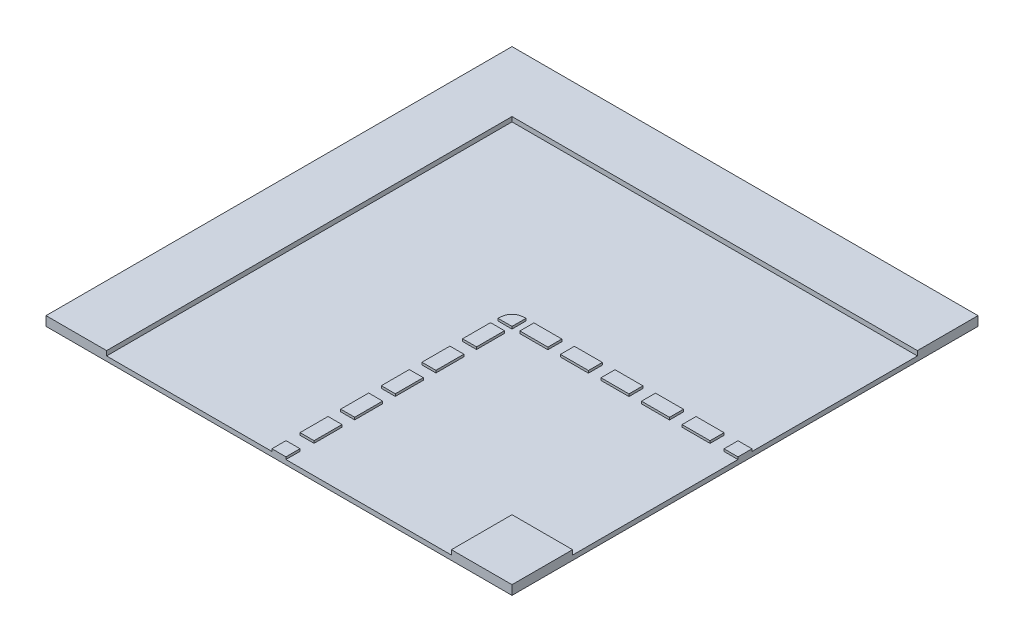
SolidWorks part; units mm, degrees
ref_plane "Plano frontal" through (0, 0, 0) normal (0, 0, 1) x (1, 0, 0)
ref_plane "Plano superior" through (0, 0, 0) normal (0, 1, 0) x (1, 0, 0)
ref_plane "Plano direito" through (0, 0, 0) normal (1, 0, 0) x (0, 0, -1)
sketch "Esboço1" plane through (0, 0, 0) normal (0, 1, 0) x (1, 0, 0)
  line L1 (-0.5, -0.5) -> (0.5, -0.5)
  line L2 (-0.5, -0.5) -> (-0.5, 0.5)
  line L3 (-0.5, 0.5) -> (0.5, 0.5)
  line L4 (0.5, -0.5) -> (0.5, 0.5)
  line L5 (-0.5, -0.5) -> (0.5, 0.5) construction
  line L6 (-0.5, 0.5) -> (0.5, -0.5) construction
  point P0 (0, 0)
  dimension "D1" = 1
  dimension "D2" = 1
sketch "Esboço2" plane through (0, 0, 0) normal (0, 1, 0) x (1, 0, 0)
  line L1 (0.5, 0.5) -> (-0.5, 0.5)
  line L2 (0.5, 0.5) -> (0.5, 0.37)
  line L3 (0.5, 0.37) -> (-0.37, 0.37)
  line L5 (-0.5, 0.5) -> (0.5, -0.5) construction
  line L6 (-0.5, -0.5) -> (-0.37, -0.5)
  line L7 (-0.5, -0.5) -> (-0.5, 0.5)
  line L8 (-0.5, 0.5) -> (-0.37, 0.5)
  line L9 (-0.37, -0.5) -> (-0.37, 0.37)
  line L10 (0.5, -0.5) -> (0.37, -0.5)
  line L11 (0.5, -0.5) -> (0.5, -0.37)
  line L12 (0.5, -0.37) -> (0.37, -0.37)
  line L13 (0.37, -0.5) -> (0.37, -0.37)
  dimension "D1" = 0.13
  dimension "D2" = 0.13
  dimension "D3" = 0.13
extrude "Ressalto-extrusão1" add sketch "Esboço1" along normal blind 0.01
extrude "Ressalto-extrusão2" add sketch "Esboço2" along normal blind 0.02 contours L7 L6 L9 L3 L2 L1 | L10 L13 L12 L11
sketch "Esboço3" plane through (0, 0.01, 0) normal (0, 1, 0) x (1, 0, 0)
  line L0 (0, 0) -> (0.4995, 0) construction
  line L1 (0, 0) -> (0, -0.5) construction
  line L2 (-0.37, -0.5) -> (0.37, -0.5) construction
  line L4 (-0.0152, -0.5) -> (-0.0152, -0.4698)
  line L5 (-0.0152, -0.4698) -> (0.0148, -0.4698)
  line L6 (0.0148, -0.5) -> (0.0148, -0.4698)
  line L7 (0, -0.5) -> (0.0148, -0.4698) construction
  line L8 (-0.0152, -0.4698) -> (0, -0.5) construction
  line L9 (-0.0152, -0.5) -> (0.0148, -0.5)
  line L10 (0, -0.53) -> (0, -0.6863) construction
  line L12 (-0.015, -0.3798) -> (0.015, -0.3798)
  line L13 (-0.015, -0.3798) -> (-0.015, -0.4398)
  line L14 (-0.015, -0.4398) -> (0.015, -0.4398)
  line L15 (0.015, -0.3798) -> (0.015, -0.4398)
  line L16 (-0.015, -0.3798) -> (0.015, -0.4398) construction
  line L17 (-0.015, -0.4398) -> (0.015, -0.3798) construction
  line L41 (-0.015, -0.015) -> (-0.015, 0.015) construction
  line L44 (-0.015, -0.015) -> (0.015, -0.015)
  line L45 (0.015, 0.015) -> (0.015, -0.015)
  line L46 (-0.015, 0.015) -> (0.015, 0.015) construction
  line L47 (0.47, 0.015) -> (0.5, 0.015)
  line L51 (0.47, -0.015) -> (0.47, 0.015)
  line L52 (0.4995, 0) -> (0.47, 0.015) construction
  line L53 (0.4995, 0) -> (0.47, -0.015) construction
  line L54 (0.5, -0.37) -> (0.5, 0.37) construction
  line L55 (0.47, -0.015) -> (0.5, -0.015)
  line L56 (0.5, -0.015) -> (0.5, 0.015)
  line L57 (0.293, -0.015) -> (0.293, 0.015)
  line L58 (0.38, -0.015) -> (0.44, -0.015)
  line L59 (0.38, -0.015) -> (0.38, 0.015)
  line L60 (0.38, 0.015) -> (0.44, 0.015)
  line L61 (0.44, -0.015) -> (0.44, 0.015)
  line L62 (0.38, -0.015) -> (0.44, 0.015) construction
  line L63 (0.38, 0.015) -> (0.44, -0.015) construction
  line L64 (0.293, -0.015) -> (0.353, -0.015)
  line L65 (0.353, -0.015) -> (0.353, 0.015)
  line L66 (0.293, 0.015) -> (0.353, 0.015)
  line L67 (0.206, -0.015) -> (0.206, 0.015)
  line L68 (0.206, -0.015) -> (0.266, -0.015)
  line L69 (0.266, -0.015) -> (0.266, 0.015)
  line L70 (0.206, 0.015) -> (0.266, 0.015)
  line L71 (0.119, -0.015) -> (0.119, 0.015)
  line L72 (0.119, -0.015) -> (0.179, -0.015)
  line L73 (0.179, -0.015) -> (0.179, 0.015)
  line L74 (0.119, 0.015) -> (0.179, 0.015)
  line L75 (0.032, -0.015) -> (0.032, 0.015)
  line L76 (0.032, -0.015) -> (0.092, -0.015)
  line L77 (0.092, -0.015) -> (0.092, 0.015)
  line L78 (0.032, 0.015) -> (0.092, 0.015)
  line L79 (-0.015, -0.2926) -> (-0.015, -0.3526)
  line L80 (-0.015, -0.2926) -> (0.015, -0.2926)
  line L81 (0.015, -0.2926) -> (0.015, -0.3526)
  line L82 (-0.015, -0.3526) -> (0.015, -0.3526)
  line L83 (-0.015, -0.2054) -> (-0.015, -0.2654)
  line L84 (-0.015, -0.2054) -> (0.015, -0.2054)
  line L85 (0.015, -0.2054) -> (0.015, -0.2654)
  line L86 (-0.015, -0.2654) -> (0.015, -0.2654)
  line L87 (-0.015, -0.1183) -> (-0.015, -0.1783)
  line L88 (-0.015, -0.1183) -> (0.015, -0.1183)
  line L89 (0.015, -0.1183) -> (0.015, -0.1783)
  line L90 (-0.015, -0.1783) -> (0.015, -0.1783)
  line L91 (-0.015, -0.0311) -> (-0.015, -0.0911)
  line L92 (-0.015, -0.0311) -> (0.015, -0.0311)
  line L93 (0.015, -0.0311) -> (0.015, -0.0911)
  line L94 (-0.015, -0.0911) -> (0.015, -0.0911)
  spline S0 degree 2 poles (-0.015, -0.015) (-0.015, 0.015) (0.015, 0.015) knots 0 0 0 1 1 1
  point P1 (0.41, 0)
  point P3 (0, -0.5)
  point P6 (0, -0.4098)
  point P43 (0.4995, 0)
  dimension "D1" = 0.03
  dimension "D2" = 0.03
  dimension "D3" = 0.03
  dimension "D5" = 0.03
  dimension "D6" = 0.03
  dimension "D7" = 0.03
  dimension "D8" = 0.03
  dimension "D9" = 0.06
  dimension "D4" = 0.06
  dimension "D10" = 5
  dimension "D11" = 5
extrude "Ressalto-extrusão4" add sketch "Esboço3" along normal blind 0.005
